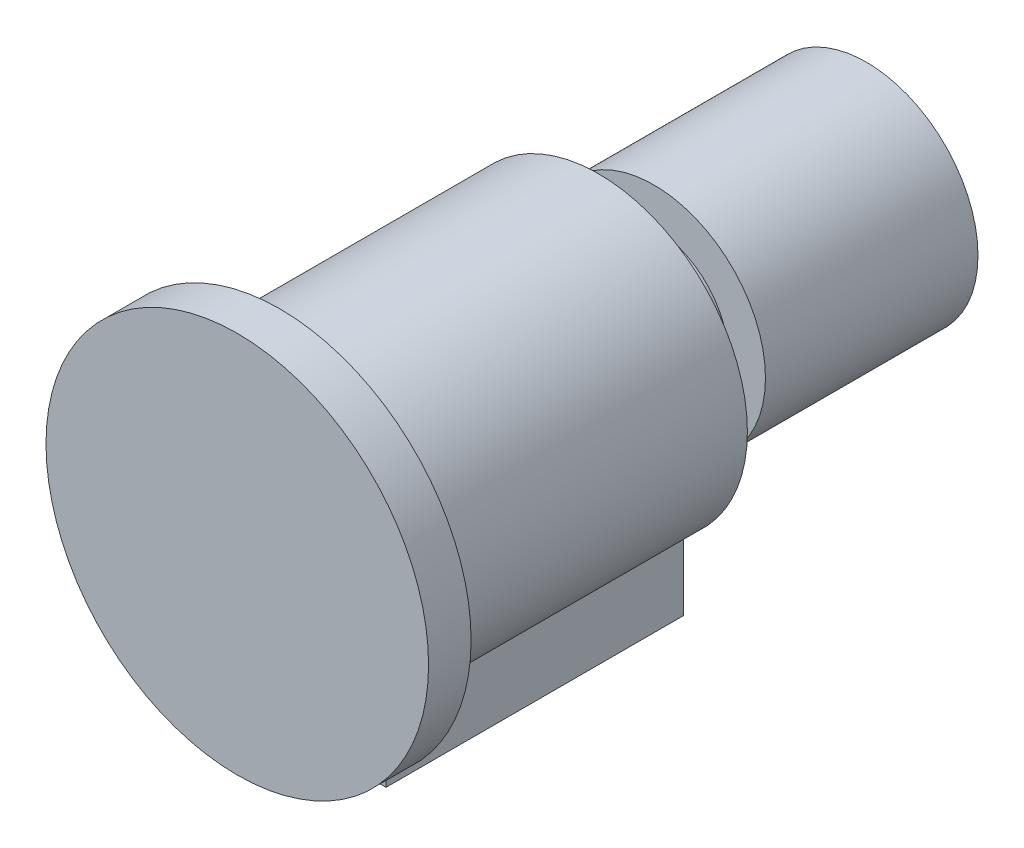
SolidWorks part; units mm, degrees
material "Plomo puro"
ref_plane "Alzado" through (0, 0, 0) normal (0, 0, 1) x (1, 0, 0)
ref_plane "Planta" through (0, 0, 0) normal (0, 1, 0) x (1, 0, 0)
ref_plane "Vista lateral" through (0, 0, 0) normal (1, 0, 0) x (0, 0, -1)
sketch "Croquis2" plane through (0, 0, 0) normal (0, 0, 1) x (1, 0, 0)
  circle A0 centre (0, 0) radius 90
  dimension "D1" = 180
extrude "Saliente-Extruir2" add sketch "Croquis2" along normal blind 20 contours A0
sketch "Croquis4" plane through (0, 0, 0) normal (0, 0, 1) x (1, 0, 0)
  circle A1 centre (0, 0) radius 70
  dimension "D1" = 140
extrude "Saliente-Extruir3" add sketch "Croquis4" against normal blind 150
ref_plane "Plano2" through (0, 0, -150) normal (0, 0, 1) x (1, 0, 0)
sketch "Croquis5" plane through (0, 0, -150) normal (0, 0, 1) x (1, 0, 0)
  circle A0 centre (0, 0) radius 35
  dimension "D1" = 70
extrude "Saliente-Extruir4" add sketch "Croquis5" against normal blind 125
ref_plane "Plano3" through (0, 0, -276) normal (0, 0, 1) x (1, 0, 0)
sketch "Croquis6" plane through (0, 0, -276) normal (0, 0, 1) x (1, 0, 0)
  circle A0 centre (0, 0) radius 52.5
extrude "Saliente-Extruir5" add sketch "Croquis6" along normal blind 100
sketch "Croquis7" plane through (0, 0, 0) normal (0, 1, 0) x (1, 0, 0)
  line L0 (0, 0) -> (0, 150) construction
  line L1 (70, 150) -> (-70, 150) construction
  line L2 (-70, 75) -> (70, 75) construction
  line L3 (-70, 150) -> (-70, 0) construction
  line L4 (70, 0) -> (70, 150) construction
  line L6 (-45, 5) -> (45, 5)
  line L7 (-45, 5) -> (-45, 145)
  line L8 (-45, 145) -> (45, 145)
  line L9 (45, 5) -> (45, 145)
  line L10 (-45, 5) -> (45, 145) construction
  line L11 (-45, 145) -> (45, 5) construction
  point P11 (0, 75)
  dimension "D1" = 140
  dimension "D2" = 90
extrude "Saliente-Extruir7" add sketch "Croquis7" against normal blind 85 contours L8 L9 L6 L7
ref_plane "Plano4" through (0, -100, 0) normal (0, 1, 0) x (1, 0, 0)
